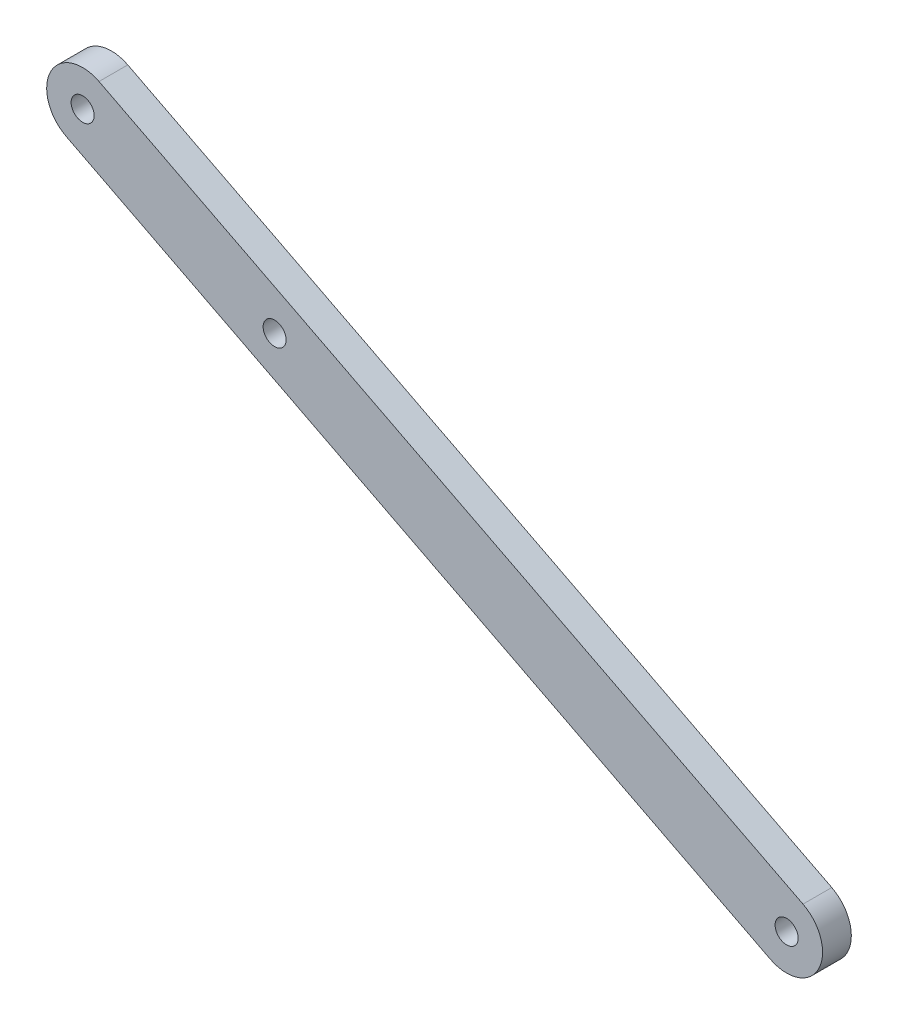
SolidWorks part; units mm, degrees
ref_plane "Front Plane" through (0, 0, 0) normal (0, 0, 1) x (1, 0, 0)
ref_plane "Top Plane" through (0, 0, 0) normal (0, 1, 0) x (1, 0, 0)
ref_plane "Right Plane" through (0, 0, 0) normal (1, 0, 0) x (0, 0, -1)
sketch "Sketch1" plane through (0, 0, 0) normal (0, 0, 1) x (1, 0, 0)
  line L0 (0, 0) -> (-97.9151, 50.1262) construction
  line L1 (-2.2785, -4.4507) -> (-100.1936, 45.6755)
  line L2 (2.2785, 4.4507) -> (-95.6366, 54.5769)
  arc A0 (-2.2785, -4.4507) -> (2.2785, 4.4507) centre (0, 0) ccw
  arc A1 (-95.6366, 54.5769) -> (-100.1936, 45.6755) centre (-97.9151, 50.1262) ccw
  circle A2 centre (-97.9151, 50.1262) radius 1.6
  circle A3 centre (0, 0) radius 1.6
  circle A5 centre (-71.211, 36.4554) radius 1.6
  point P3 (-48.9576, 25.0631)
  dimension "D3" = 3.2
  dimension "D1" = 10
  dimension "D2" = 110
  dimension "D4" = 30
extrude "Boss-Extrude1" add sketch "Sketch1" along normal blind 4
